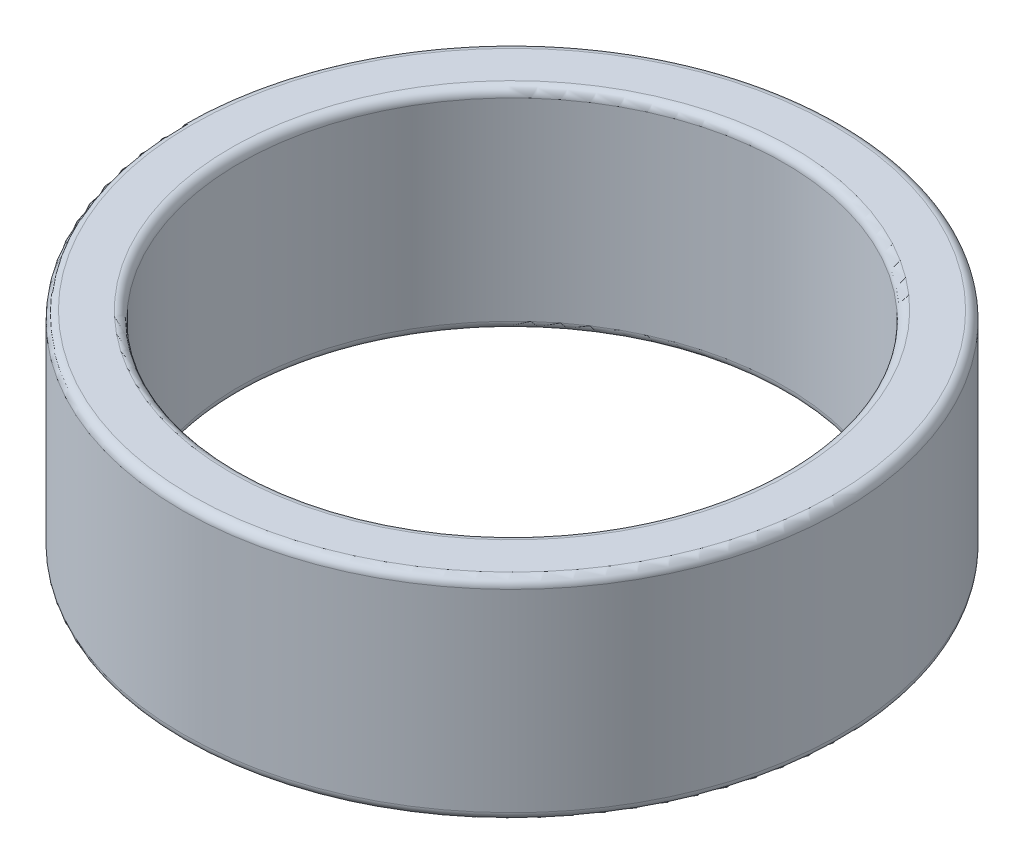
SolidWorks part; units mm, degrees
ref_plane "Plan de face" through (0, 0, 0) normal (0, 0, 1) x (1, 0, 0)
ref_plane "Plan de dessus" through (0, 0, 0) normal (0, 1, 0) x (1, 0, 0)
ref_plane "Plan de droite" through (0, 0, 0) normal (1, 0, 0) x (0, 0, -1)
sketch "Esquisse1" plane through (0, 0, 0) normal (0, 1, 0) x (1, 0, 0)
  circle A0 centre (0, 0) radius 18.75
  circle A1 centre (0, 0) radius 15.5
extrude "Boss.-Extru.1" add sketch "Esquisse1" along normal blind 12
fillet "Congé1" radius 0.5 4 edges at (0, 0, 15.5) (0, 0, 18.75) (0, 12, 15.5) (0, 12, 18.75)
